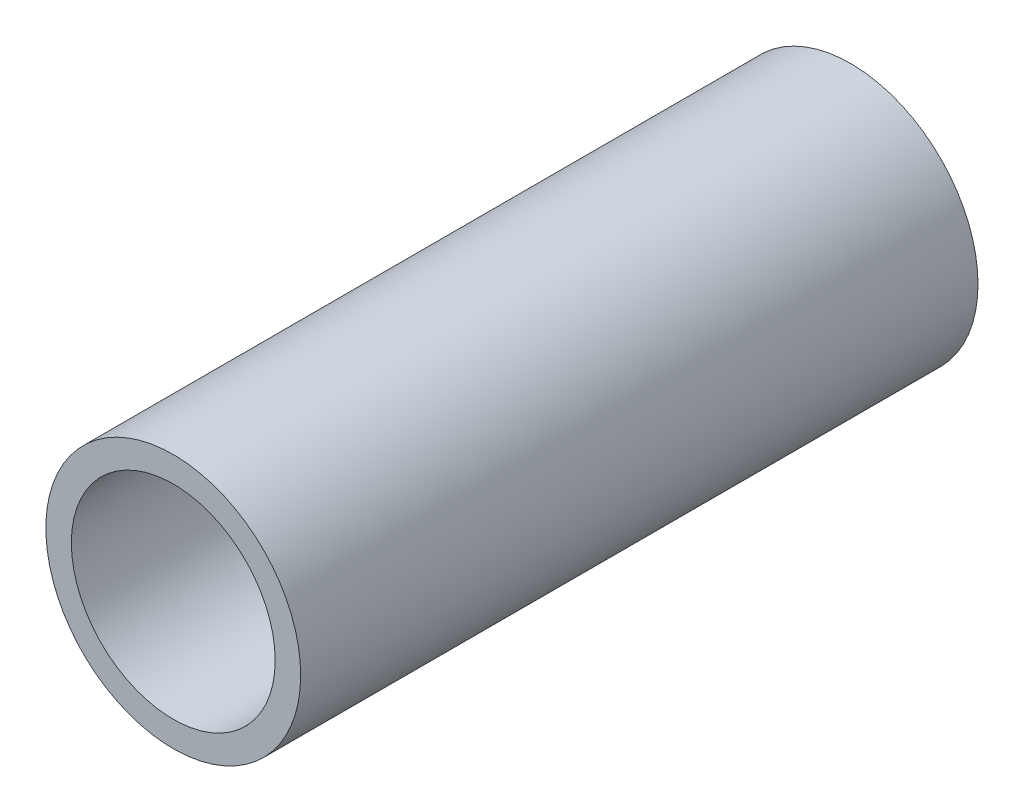
SolidWorks part; units mm, degrees
ref_plane "Front Plane" through (0, 0, 0) normal (0, 0, 1) x (1, 0, 0)
ref_plane "Top Plane" through (0, 0, 0) normal (0, 1, 0) x (1, 0, 0)
ref_plane "Right Plane" through (0, 0, 0) normal (1, 0, 0) x (0, 0, -1)
sketch "Sketch1" plane through (0, 0, 0) normal (0, 0, 1) x (1, 0, 0)
  circle A0 centre (0, 0) radius 1.25
  circle A1 centre (0, 0) radius 1
extrude "Boss-Extrude1" add sketch "Sketch1" along normal blind 6.645
equation "\"D1@Boss-Extrude1\"= \"HL@parametersSketch@prostheticParameters.SLDPRT\" * 0.117 - 2 - 3 - 10 'Pinky MIP Tube"
